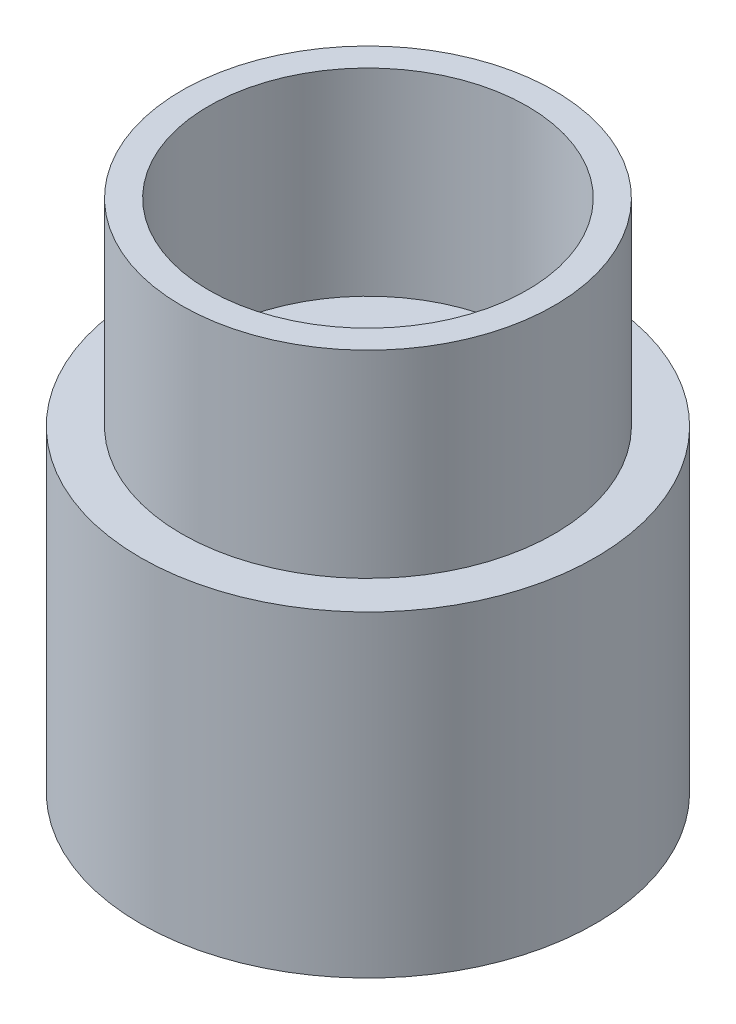
SolidWorks part; units mm, degrees
ref_plane "Alzado" through (0, 0, 0) normal (0, 0, 1) x (1, 0, 0)
ref_plane "Planta" through (0, 0, 0) normal (0, 1, 0) x (1, 0, 0)
ref_plane "Vista lateral" through (0, 0, 0) normal (1, 0, 0) x (0, 0, -1)
sketch "Croquis1" plane through (0, 0, 0) normal (0, 1, 0) x (1, 0, 0)
  circle A0 centre (0, 0) radius 9.05
  circle A1 centre (0, 0) radius 11.05
  dimension "D1" = 18.1
  dimension "D2" = 2
extrude "Saliente-Extruir1" add sketch "Croquis1" against normal blind 9.4
sketch "Croquis2" plane through (0, 0, 0) normal (0, 1, 0) x (1, 0, 0)
  circle A2 centre (0, 0) radius 11.05
  circle A3 centre (0, 0) radius 11.05
  dimension "D1" = 0
extrude "Saliente-Extruir2" add sketch "Croquis2" along normal blind 6
sketch "Croquis3" plane through (0, 6, 0) normal (0, 1, 0) x (1, 0, 0)
  circle A0 centre (0, 0) radius 7.74
  circle A1 centre (0, 0) radius 9.05
  dimension "D1" = 15.48
  dimension "D2" = 18.1
extrude "Saliente-Extruir3" add sketch "Croquis3" along normal blind 9.6
sketch "Croquis4" plane through (0, 6, 0) normal (0, 1, 0) x (1, 0, 0)
  circle A1 centre (0, 0) radius 3.05
  dimension "D1" = 6.1
extrude "Cortar-Extruir1" cut sketch "Croquis4" against normal blind 9.6
sketch "Croquis5" plane through (0, -9.4, 0) normal (0, -1, 0) x (1, 0, 0)
  circle A0 centre (0, 0) radius 9.15
  circle A1 centre (0, 0) radius 9.05 construction
  dimension "D1" = 0.1
extrude "Cortar-Extruir2" cut sketch "Croquis5" against normal up to surface (9.4 mm away) up to face at (0, 0, 3.05)
sketch "Croquis6" plane through (0, 0, 0) normal (0, 0, 1) x (1, 0, 0)
  line L0 (-9.15, 0) -> (-7.6434, 1.5066)
  line L1 (-9.15, 0) -> (9.15, 0) construction
  line L2 (-7.6434, 1.5066) -> (-5.1722, 1.5066)
  line L3 (0, 1.5066) -> (0, 0)
  line L4 (0, 0) -> (-9.15, 0)
  line L5 (-5.1722, 1.5066) -> (-3.05, 6)
  line L6 (11.05, 6) -> (-11.05, 6) construction
  line L7 (3.05, 6) -> (-3.05, 6) construction
  line L8 (-3.05, 6) -> (0, 6)
  line L9 (0, 6) -> (0, 1.5066)
revolve "Cortar-Revolución1" cut sketch "Croquis6" angle 360 about L3
